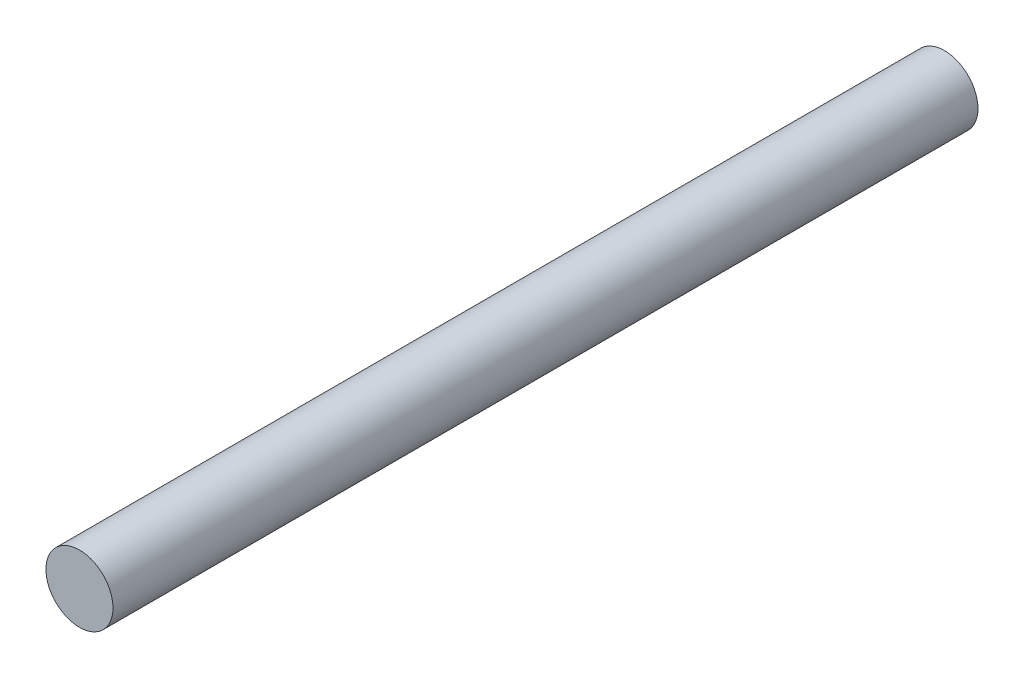
SolidWorks part; units mm, degrees
ref_plane "Front Plane" through (0, 0, 0) normal (0, 0, 1) x (1, 0, 0)
ref_plane "Top Plane" through (0, 0, 0) normal (0, 1, 0) x (1, 0, 0)
ref_plane "Right Plane" through (0, 0, 0) normal (1, 0, 0) x (0, 0, -1)
sketch "Sketch1" plane through (0, 0, 0) normal (0, 0, 1) x (1, 0, 0)
  circle A0 centre (0, 0) radius 1
  dimension "D1" = 2
extrude "Boss-Extrude1" add sketch "Sketch1" along normal blind 25.8
